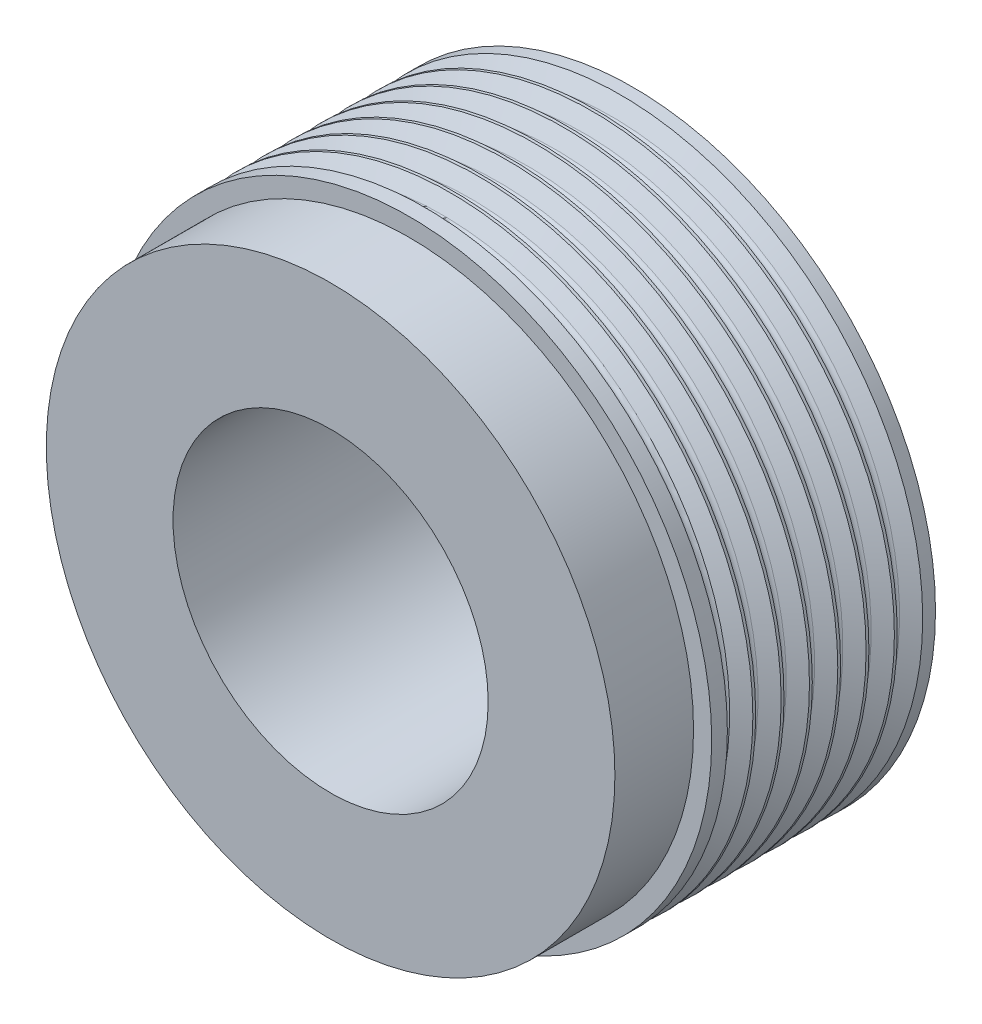
SolidWorks part; units mm, degrees
ref_plane "前视基准面" through (0, 0, 0) normal (0, 0, 1) x (1, 0, 0)
ref_plane "上视基准面" through (0, 0, 0) normal (0, 1, 0) x (1, 0, 0)
ref_plane "右视基准面" through (0, 0, 0) normal (1, 0, 0) x (0, 0, -1)
other "Configuration Table"
sketch "草图1" plane through (0, 0, 0) normal (0, 0, 1) x (1, 0, 0)
  circle A0 centre (0, 0) radius 25
  dimension "D1" = 50
extrude "凸台-拉伸1" add sketch "草图1" along normal blind 25
sketch "草图2" plane through (0, 0, 25) normal (0, 0, 1) x (1, 0, 0)
  circle A1 centre (0, 0) radius 25 construction
  circle A2 centre (0, 0) radius 23.5
  circle A3 centre (0, 0) radius 23.5
  circle A4 centre (0, 0) radius 25
  dimension "D1" = 1.5
extrude "切除-拉伸1" cut sketch "草图2" against normal blind 6.5
sketch "草图3" plane through (0, 0, 25) normal (0, 0, 1) x (1, 0, 0)
  circle A0 centre (0, 0) radius 13.025
  dimension "D1" = 26.05
extrude "切除-拉伸2" cut sketch "草图3" against normal blind 25
sketch "草图4" plane through (0, 0, 0) normal (1, 0, 0) x (0, 0, -1)
  line L0 (-1.5, 27.169) -> (-1.5, 25.2) construction
  line L1 (-3.223, 25.1) -> (-1, 25.1)
  line L2 (-5.563, 25.1) -> (-3.34, 25.1)
  line L3 (-4.7968, 23.7902) -> (-5.563, 25.1)
  line L4 (0, -25) -> (0, 25) construction
  line L5 (-1, 25.1) -> (-1.7662, 23.7902)
  line L6 (-0.3942, 25.2) -> (-6.5605, 25.2) construction
  line L7 (-2.4568, 23.7902) -> (-3.223, 25.1)
  line L8 (-2.67, 23.2) -> (-2.67, 25.2) construction
  line L9 (-3.34, 25.1) -> (-4.1062, 23.7902)
  line L10 (-3.84, 25.2) -> (-1.5, 25.2) construction
  line L32 (0, 0) -> (-25, 0) construction
  line L33 (-25, 23.5) -> (-25, -23.5) construction
  line L34 (0, 25) -> (-18.5, 25) construction
  line L35 (-7.903, 25.1) -> (-5.68, 25.1)
  line L36 (-7.1368, 23.7902) -> (-7.903, 25.1)
  line L37 (-5.68, 25.1) -> (-6.4462, 23.7902)
  line L38 (-10.243, 25.1) -> (-8.02, 25.1)
  line L39 (-9.4768, 23.7902) -> (-10.243, 25.1)
  line L40 (-8.02, 25.1) -> (-8.7862, 23.7902)
  line L41 (-12.583, 25.1) -> (-10.36, 25.1)
  line L42 (-11.8168, 23.7902) -> (-12.583, 25.1)
  line L43 (-10.36, 25.1) -> (-11.1262, 23.7902)
  line L44 (-14.923, 25.1) -> (-12.7, 25.1)
  line L45 (-14.1568, 23.7902) -> (-14.923, 25.1)
  line L46 (-12.7, 25.1) -> (-13.4662, 23.7902)
  line L47 (-17.263, 25.1) -> (-15.04, 25.1)
  line L48 (-16.4968, 23.7902) -> (-17.263, 25.1)
  line L49 (-15.04, 25.1) -> (-15.8062, 23.7902)
  line L53 (-1, 26.6505) -> (-1, 20.8469) construction
  line L54 (-19.603, 25.1) -> (-17.38, 25.1) [skipped]
  line L55 (-18.8368, 23.7902) -> (-19.603, 25.1) [skipped]
  line L56 (-17.38, 25.1) -> (-18.1462, 23.7902) [skipped]
  arc A0 (-2.4568, 23.7902) -> (-1.7662, 23.7902) centre (-2.1115, 23.9922) ccw
  arc A1 (-4.7968, 23.7902) -> (-4.1062, 23.7902) centre (-4.4515, 23.9922) ccw
  arc A2 (-7.1368, 23.7902) -> (-6.4462, 23.7902) centre (-6.7915, 23.9922) ccw
  arc A3 (-9.4768, 23.7902) -> (-8.7862, 23.7902) centre (-9.1315, 23.9922) ccw
  arc A4 (-11.8168, 23.7902) -> (-11.1262, 23.7902) centre (-11.4715, 23.9922) ccw
  arc A5 (-14.1568, 23.7902) -> (-13.4662, 23.7902) centre (-13.8115, 23.9922) ccw
  arc A6 (-16.4968, 23.7902) -> (-15.8062, 23.7902) centre (-16.1515, 23.9922) ccw
  arc A8 (-18.8368, 23.7902) -> (-18.1462, 23.7902) centre (-18.4915, 23.9922) ccw [skipped]
  dimension "D3" = 2
  dimension "D4" = 0.4
  dimension "D1" = 1.5
  dimension "D2" = 2.34
  dimension "D5" = 0.2
  dimension "D7" = 0.1
  dimension "D9" = 1
  dimension "D8" = 8
revolve "切除-旋转2" cut sketch "草图4" angle 360 about L32
